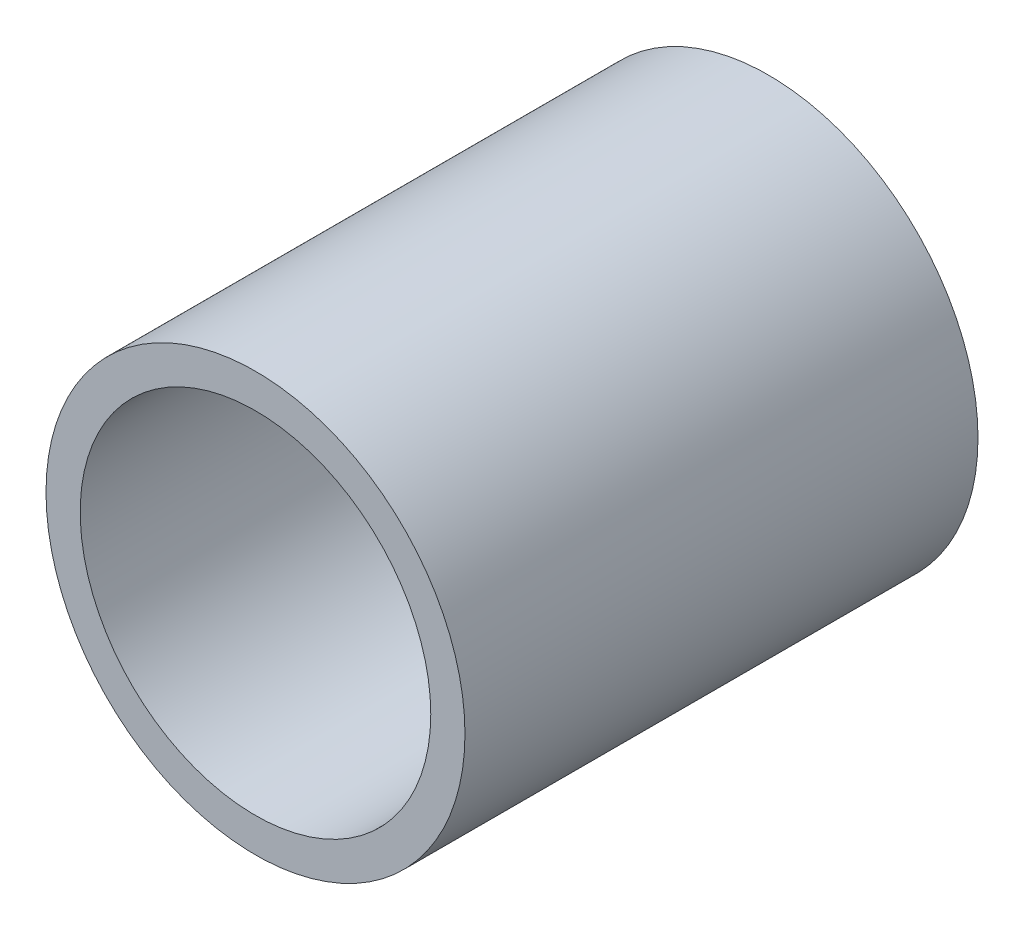
SolidWorks part; units mm, degrees
material "ABS"
ref_plane "Front Plane" through (0, 0, 0) normal (0, 0, 1) x (1, 0, 0)
ref_plane "Top Plane" through (0, 0, 0) normal (0, 1, 0) x (1, 0, 0)
ref_plane "Right Plane" through (0, 0, 0) normal (1, 0, 0) x (0, 0, -1)
sketch "Sketch1" plane through (0, 0, 0) normal (0, 0, 1) x (1, 0, 0)
  circle A0 centre (0, 0) radius 6.125
  circle A1 centre (0, 0) radius 5.125
  dimension "D1" = 10.25
  dimension "D2" = 12.25
extrude "Boss-Extrude1" add sketch "Sketch1" along normal blind 15
